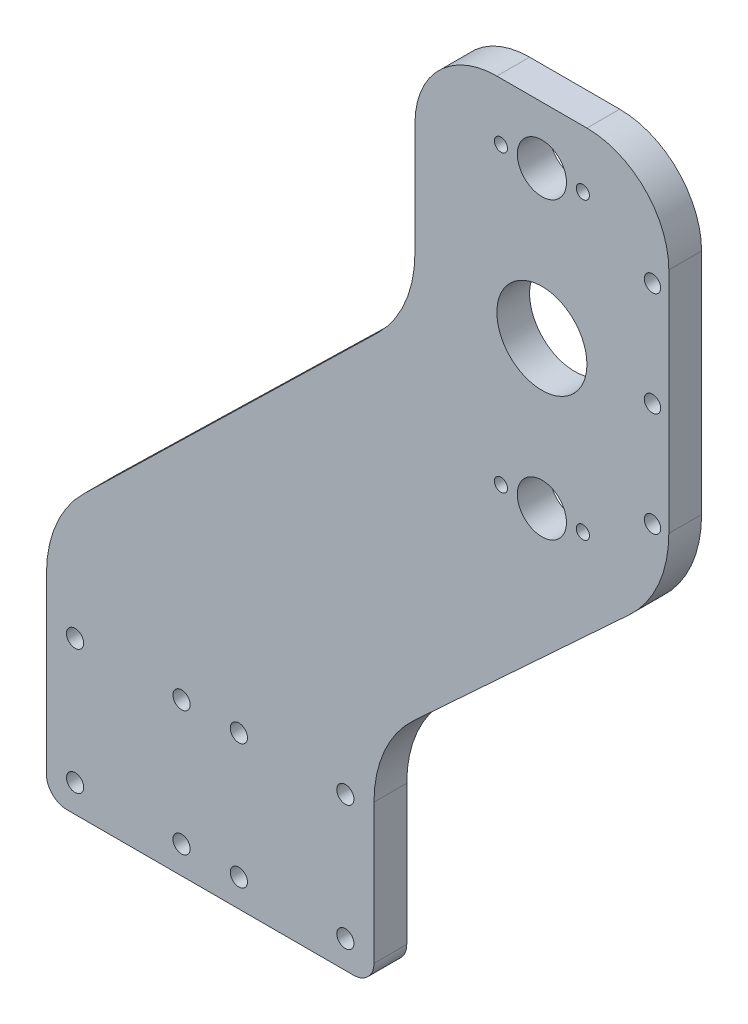
SolidWorks part; units mm, degrees
ref_plane "Front Plane" through (0, 0, 0) normal (0, 0, 1) x (1, 0, 0)
ref_plane "Top Plane" through (0, 0, 0) normal (0, 1, 0) x (1, 0, 0)
ref_plane "Right Plane" through (0, 0, 0) normal (1, 0, 0) x (0, 0, -1)
sketch "Sketch1" plane through (0, 0, 0) normal (0, 0, 1) x (1, 0, 0)
  line L0 (-23.6346, -94.316) -> (-23.6346, -15.4242) construction
  line L1 (-58.6346, -94.316) -> (11.3654, -94.316)
  line L2 (-63.6346, -89.316) -> (-63.6346, -46.974)
  line L3 (-63.6346, -89.316) -> (-23.6346, -89.316) construction
  line L4 (16.3654, -89.316) -> (16.3654, -55.2061)
  line L5 (46.3654, 113.3484) -> (68.3654, 113.3484)
  line L6 (26.3654, 93.3484) -> (26.3654, 66.0064)
  line L7 (57.3654, 113.3484) -> (57.3654, 27.4084) construction
  line L8 (88.3654, 93.3484) -> (88.3654, 37.6266)
  line L9 (-43.6346, -72.316) -> (-43.6346, -89.316) construction
  line L10 (-56.6346, -57.066) -> (-30.6346, -57.066) construction
  line L11 (17.2979, 44.5162) -> (-54.5671, -25.4838)
  line L12 (78.7367, 15.6036) -> (25.9942, -33.1831)
  line L13 (-56.6346, -57.066) -> (-56.6346, -87.566) construction
  line L14 (-56.6346, -87.566) -> (-30.6346, -87.566) construction
  line L15 (-30.6346, -57.066) -> (-30.6346, -87.566) construction
  line L16 (-56.6346, -57.066) -> (-30.6346, -87.566) construction
  line L17 (-56.6346, -87.566) -> (-30.6346, -57.066) construction
  line L18 (57.3654, 99.3484) -> (57.3654, 27.4084) construction
  arc A0 (78.7367, 15.6036) -> (88.3654, 37.6266) centre (58.3654, 37.6266) ccw
  arc A1 (17.2979, 44.5162) -> (26.3654, 66.0064) centre (-3.6346, 66.0064) ccw
  arc A2 (16.3654, -55.2061) -> (25.9942, -33.1831) centre (46.3654, -55.2061) cw
  arc A3 (-63.6346, -46.974) -> (-54.5671, -25.4838) centre (-33.6346, -46.974) cw
  arc A4 (88.3654, 93.3484) -> (68.3654, 113.3484) centre (68.3654, 93.3484) ccw
  arc A5 (46.3654, 113.3484) -> (26.3654, 93.3484) centre (46.3654, 93.3484) ccw
  arc A6 (16.3654, -89.316) -> (11.3654, -94.316) centre (11.3654, -89.316) cw
  arc A7 (-58.6346, -94.316) -> (-63.6346, -89.316) centre (-58.6346, -89.316) cw
  circle A8 centre (-56.6346, -57.066) radius 2.1
  circle A9 centre (-30.6346, -57.066) radius 2.1
  circle A10 centre (-30.6346, -87.566) radius 2.1
  circle A11 centre (-56.6346, -87.566) radius 2.1
  circle A12 centre (9.3654, -87.566) radius 2.1
  circle A13 centre (-16.6346, -87.566) radius 2.1
  circle A14 centre (-16.6346, -57.066) radius 2.1
  circle A15 centre (9.3654, -57.066) radius 2.1
  circle A16 centre (57.3654, 99.3484) radius 6
  circle A17 centre (57.3654, 27.4084) radius 6
  circle A18 centre (57.3654, 63.3784) radius 11
  circle A19 centre (84.3654, 37.6266) radius 2
  circle A20 centre (84.3759, 88.5283) radius 2
  circle A21 centre (47.3654, 99.3484) radius 1.6
  circle A22 centre (47.3654, 27.4084) radius 1.6
  circle A23 centre (67.3654, 99.3484) radius 1.6
  circle A24 centre (67.3654, 27.4084) radius 1.6
  circle A25 centre (84.3707, 63.0775) radius 2
  point P0 (0, 0)
  point P1 (57.3654, 82.2289)
  point P15 (26.3654, 53.3484)
  point P20 (-63.6346, -34.316)
  point P23 (88.3654, 113.3484)
  point P26 (26.3654, 113.3484)
  point P29 (16.3654, -94.316)
  point P32 (-63.6346, -94.316)
  point P35 (-43.6346, -72.316)
  dimension "D5" = 30
  dimension "D6" = 20
  dimension "D7" = 5
  dimension "D14" = 71.94
  dimension "D12" = 4
  dimension "D16" = 10
  dimension "D17" = 10
  dimension "D1" = 80
  dimension "D2" = 22
  dimension "D3" = 90
  dimension "D4" = 60
  dimension "D8" = 26
  dimension "D9" = 60
  dimension "D10" = 22
  dimension "D11" = 70
  dimension "D13" = 30.5
  dimension "D15" = 14
extrude "Boss-Extrude1" add sketch "Sketch1" along normal blind 8 contours L11 A3 L2 A7 L1 A6 L4 A2 L12 A0 L8 A4 L5 A5 L6 A1
